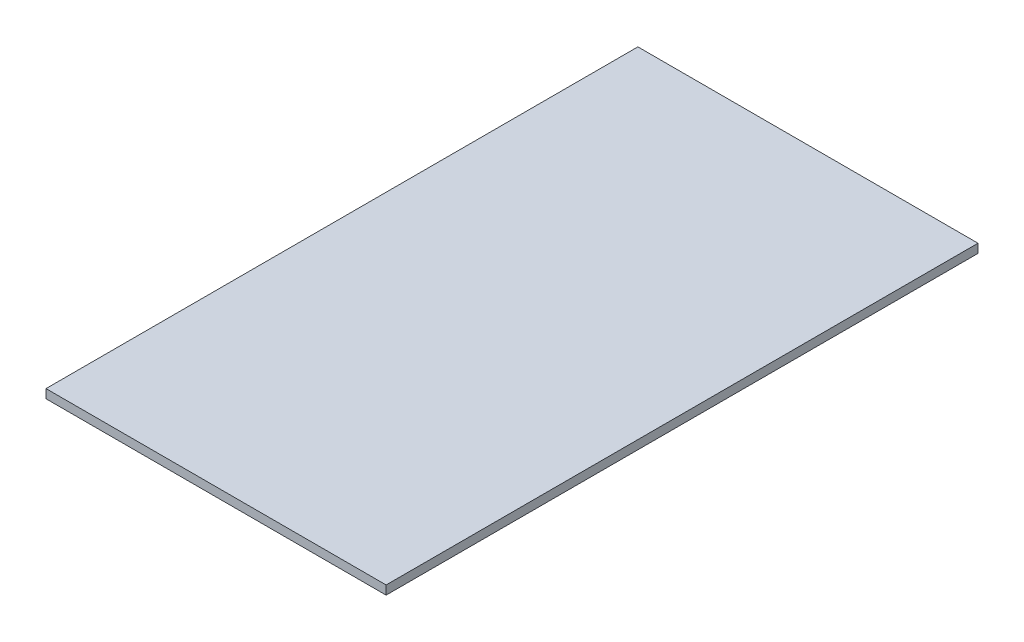
SolidWorks part; units mm, degrees
ref_plane "Plan de face" through (0, 0, 0) normal (0, 0, 1) x (1, 0, 0)
ref_plane "Plan de dessus" through (0, 0, 0) normal (0, 1, 0) x (1, 0, 0)
ref_plane "Plan de droite" through (0, 0, 0) normal (1, 0, 0) x (0, 0, -1)
sketch "Esquisse1" plane through (0, 0, 0) normal (0, 1, 0) x (1, 0, 0)
  line L1 (-87.9452, 33.8156) -> (297.0548, 33.8156)
  line L2 (-87.9452, 33.8156) -> (-87.9452, -636.1844)
  line L3 (-87.9452, -636.1844) -> (297.0548, -636.1844)
  line L4 (297.0548, 33.8156) -> (297.0548, -636.1844)
  dimension "D1" = 385
  dimension "D2" = 670
extrude "Boss.-Extru.1" add sketch "Esquisse1" along normal blind 10
equation "\"EpaisseurPlaque\"= 10"
equation "\"D1@Boss.-Extru.1\"=\"EpaisseurPlaque\""
equation "\"ProfondeurPlacard\"=580"
equation "\"LargeurPlacard\"=160+70+135"
equation "\"DistanceAvantSyphon\"=240"
equation "\"DistanceAvantEvier\"=100"
equation "\"DiametreTuyau\"=90"
equation "\"HauteurTuyau\"=430"
equation "\"LargeurAeration\"=260"
equation "\"HauteurAeration\"=340"
equation "\"AerationSol\"=210"
equation "\"AerationAvant\"=270"
equation "\"ProfondeurCharniere\"=80"
equation "\"HauteurCharniere\"=60"
equation "\"LargeurCharniere\"=60"
equation "\"HauteurPlacard\"=650"
equation "\"HauteurEvier\"=\"HauteurPlacard\"-555"
equation "\"HauteurDroitEvier\"=\"HauteurPlacard\" -500"
equation "\"HauteurSolSyphon\"=320"
equation "\"DiametreSyphon\"=70"
equation "\"PositionSyphonCoteGauche\"=160"
equation "\"D1@Esquisse1\"=\"LargeurPlacard\" + \"EpaisseurPlaque\"*2mm"
equation "\"D2@Esquisse1\"=\"HauteurPlacard\"+\"EpaisseurPlaque\"+\"EpaisseurPlaque\""
